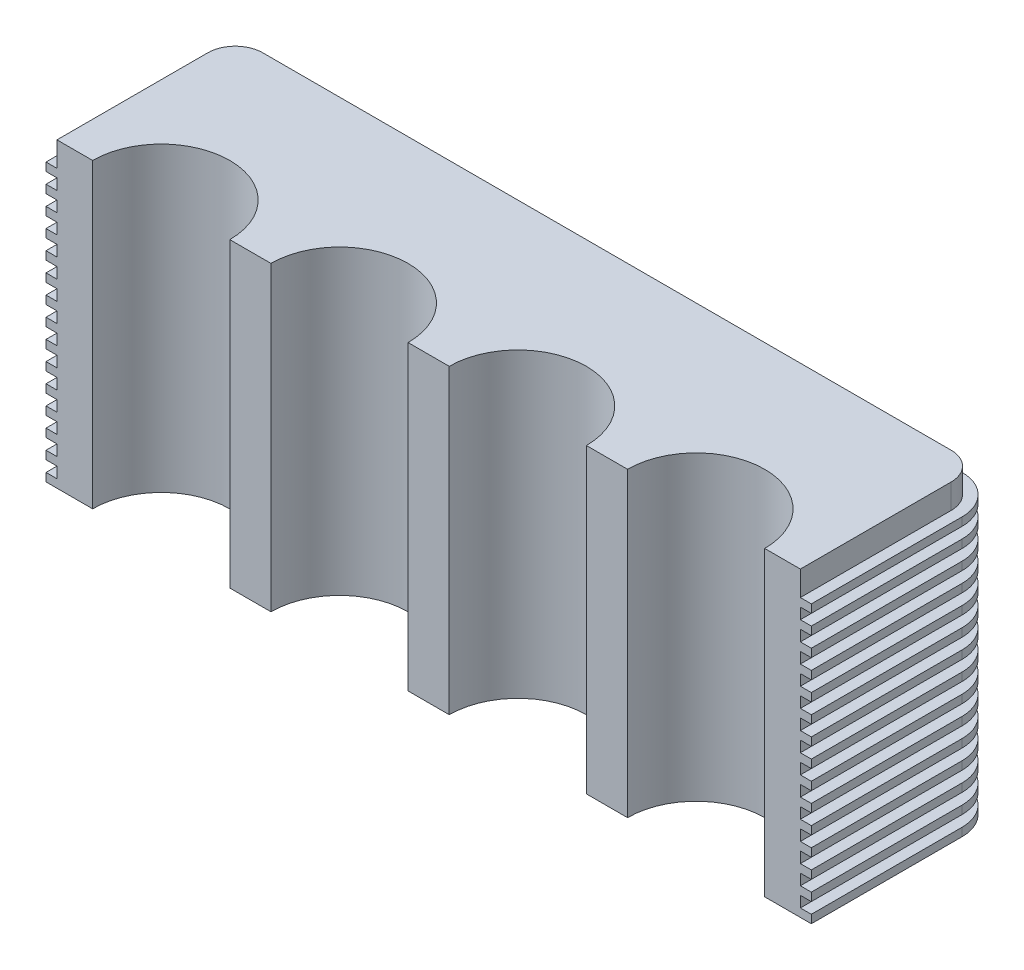
SolidWorks part; units mm, degrees
ref_plane "Front Plane" through (0, 0, 0) normal (0, 0, 1) x (1, 0, 0)
ref_plane "Top Plane" through (0, 0, 0) normal (0, 1, 0) x (1, 0, 0)
ref_plane "Right Plane" through (0, 0, 0) normal (1, 0, 0) x (0, 0, -1)
sketch "Sketch1" plane through (0, 0, 0) normal (0, 1, 0) x (1, 0, 0)
  line L0 (135.5, 0) -> (135.5, 65) construction
  line L1 (0, 0) -> (13, 0)
  line L2 (0, 0) -> (0, 55)
  line L3 (10, 65) -> (261, 65)
  line L4 (271, 0) -> (271, 55)
  line L5 (258, 0) -> (271, 0)
  line L6 (193, 0) -> (208, 0)
  line L7 (63, 0) -> (78, 0)
  line L8 (128, 0) -> (143, 0)
  arc A0 (261, 65) -> (271, 55) centre (261, 55) cw
  arc A1 (0, 55) -> (10, 65) centre (10, 55) cw
  arc A2 (258, 0) -> (208, 0) centre (233, 0) ccw
  arc A3 (193, 0) -> (143, 0) centre (168, 0) ccw
  arc A4 (13, 0) -> (63, 0) centre (38, 0) cw
  arc A5 (78, 0) -> (128, 0) centre (103, 0) cw
  dimension "D1" = 10
  dimension "D4" = 25
  dimension "D6" = 50
  dimension "D2" = 271
  dimension "D3" = 65
  dimension "D5" = 13
  dimension "D7" = 15
extrude "Boss-Extrude1" add sketch "Sketch1" along normal blind 110
sketch "Sketch2" plane through (0, 0, 0) normal (0, 1, 0) x (1, 0, 0)
  line L0 (271, 0) -> (271, 55) construction
  line L1 (261, 65) -> (10, 65) construction
  line L2 (0, 55) -> (0, 0) construction
  line L3 (271, 0) -> (271, 55)
  line L4 (261, 65) -> (10, 65)
  line L5 (0, 55) -> (0, 0)
  line L6 (275, 0) -> (275, 55)
  line L7 (261, 69) -> (10, 69)
  line L8 (-4, 55) -> (-4, 0)
  line L9 (271, 0) -> (275, 0)
  line L10 (0, 0) -> (-4, 0)
  arc A0 (271, 55) -> (261, 65) centre (261, 55) ccw construction
  arc A1 (10, 65) -> (0, 55) centre (10, 55) ccw construction
  arc A2 (271, 55) -> (261, 65) centre (261, 55) ccw
  arc A3 (10, 65) -> (0, 55) centre (10, 55) ccw
  arc A4 (275, 55) -> (261, 69) centre (261, 55) ccw
  arc A5 (10, 69) -> (-4, 55) centre (10, 55) ccw
  dimension "D1" = 4
extrude "Boss-Extrude2" add sketch "Sketch2" along normal blind 3
pattern_linear "LPattern2" count 15 spacing 7 along (0, 1, 0) of "Boss-Extrude2"
